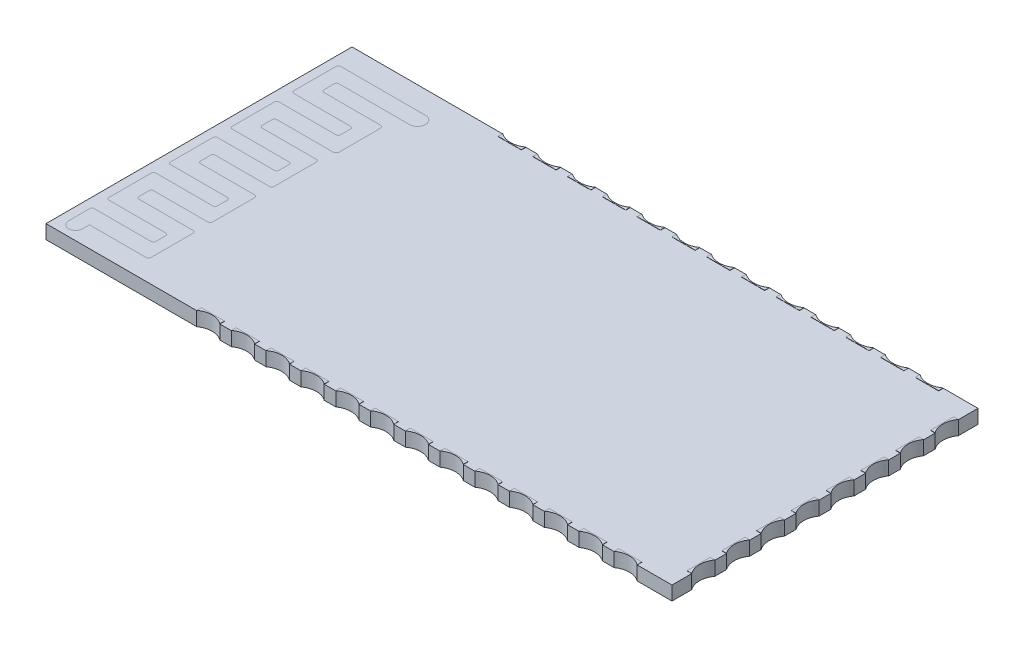
SolidWorks part; units mm, degrees
ref_plane "Front Plane" through (0, 0, 0) normal (0, 0, 1) x (1, 0, 0)
ref_plane "Top Plane" through (0, 0, 0) normal (0, 1, 0) x (1, 0, 0)
ref_plane "Right Plane" through (0, 0, 0) normal (1, 0, 0) x (0, 0, -1)
sketch "Sketch1" plane through (0, 0, 0) normal (0, 1, 0) x (1, 0, 0)
  line L1 (-13.5, -6.6) -> (13.5, -6.6)
  line L2 (-13.5, -6.6) -> (-13.5, 6.6)
  line L3 (-13.5, 6.6) -> (13.5, 6.6)
  line L4 (13.5, -6.6) -> (13.5, 6.6)
  line L5 (-13.5, -6.6) -> (13.5, 6.6) construction
  line L6 (-13.5, 6.6) -> (13.5, -6.6) construction
  point P0 (0, 0)
  dimension "D1" = 13.2
  dimension "D2" = 27
extrude "Boss-Extrude1" add sketch "Sketch1" along normal blind 0.6
sketch "Sketch2" plane through (0, 0.6, 0) normal (0, 1, 0) x (1, 0, 0)
  line L0 (-13.1181, -6.0063) -> (-13.1181, -5.0988)
  line L1 (-13.0181, -4.9988) -> (-10.5664, -4.9988)
  line L2 (-10.4664, -4.8988) -> (-10.4664, -4.4665)
  line L3 (-12.5181, -6.0063) -> (-12.5181, -5.7063)
  line L4 (-12.5181, -5.7063) -> (-10.0692, -5.7063)
  line L5 (-9.9692, -5.6063) -> (-9.9692, -3.7819)
  line L6 (-10.5664, -4.3665) -> (-13.0181, -4.3665)
  line L7 (-13.1181, -4.2665) -> (-13.1181, -2.4422)
  line L8 (-10.0692, -3.6819) -> (-12.4068, -3.6819)
  line L9 (-12.5068, -3.5819) -> (-12.5068, -3.1496)
  line L10 (-12.4068, -3.0496) -> (-10.0692, -3.0496)
  line L11 (-9.9692, -2.9496) -> (-9.9692, -1.1253)
  line L12 (-13.0181, -2.3422) -> (-10.5664, -2.3422)
  line L13 (-10.4664, -2.2422) -> (-10.4664, -1.8099)
  line L14 (-10.0692, -1.0253) -> (-12.4068, -1.0253)
  line L15 (-10.5664, -1.7099) -> (-13.0181, -1.7099)
  line L16 (-12.5068, -0.9253) -> (-12.5068, -0.493)
  line L17 (-13.1181, -1.6099) -> (-13.1181, 0.2145)
  line L18 (-13.0181, 0.3145) -> (-10.5664, 0.3145)
  line L19 (-12.4068, -0.393) -> (-10.0692, -0.393)
  line L20 (-9.9692, -0.293) -> (-9.9692, 1.5314)
  line L21 (-10.4664, 0.4145) -> (-10.4664, 0.8468)
  line L22 (-10.0692, 1.6314) -> (-12.4068, 1.6314)
  line L23 (-10.5664, 0.9468) -> (-13.0181, 0.9468)
  line L24 (-12.5068, 1.7314) -> (-12.5068, 2.1637)
  line L25 (-13.1181, 1.0468) -> (-13.1181, 2.8711)
  line L26 (-13.0181, 2.9711) -> (-10.5664, 2.9711)
  line L27 (-12.4068, 2.2637) -> (-9.9956, 2.2637)
  line L28 (-9.8488, 2.3826) -> (-9.8488, 4.2077)
  line L29 (-10.4664, 3.0711) -> (-10.4664, 3.5035)
  line L30 (-9.9832, 4.2909) -> (-12.4068, 4.2909)
  line L31 (-10.5664, 3.6035) -> (-13.0181, 3.6035)
  line L32 (-12.5068, 4.3909) -> (-12.5068, 4.8232)
  line L33 (-13.1181, 3.7035) -> (-13.1181, 5.5278)
  line L34 (-13.0181, 5.6278) -> (-9.358, 5.6278)
  line L35 (-12.4084, 4.9408) -> (-9.358, 4.9408)
  arc A0 (-13.1181, -6.0063) -> (-12.5181, -6.0063) centre (-12.8181, -6.0063) ccw
  arc A1 (-10.0692, -5.7063) -> (-9.9692, -5.6063) centre (-10.0692, -5.6063) ccw
  arc A2 (-13.1181, -5.0988) -> (-13.0181, -4.9988) centre (-13.0181, -5.0988) cw
  arc A3 (-10.5664, -4.9988) -> (-10.4664, -4.8988) centre (-10.5664, -4.8988) ccw
  arc A4 (-10.4664, -4.4665) -> (-10.5664, -4.3665) centre (-10.5664, -4.4665) ccw
  arc A5 (-9.9692, -3.7819) -> (-10.0692, -3.6819) centre (-10.0692, -3.7819) ccw
  arc A6 (-13.0181, -4.3665) -> (-13.1181, -4.2665) centre (-13.0181, -4.2665) cw
  arc A7 (-10.5664, -2.3422) -> (-10.4664, -2.2422) centre (-10.5664, -2.2422) ccw
  arc A8 (-10.0692, -3.0496) -> (-9.9692, -2.9496) centre (-10.0692, -2.9496) ccw
  arc A9 (-12.4068, -3.6819) -> (-12.5068, -3.5819) centre (-12.4068, -3.5819) cw
  arc A10 (-12.5068, -3.1496) -> (-12.4068, -3.0496) centre (-12.4068, -3.1496) cw
  arc A11 (-13.1181, -2.4422) -> (-13.0181, -2.3422) centre (-13.0181, -2.4422) cw
  arc A12 (-10.4664, -1.8099) -> (-10.5664, -1.7099) centre (-10.5664, -1.8099) ccw
  arc A13 (-9.9692, -1.1253) -> (-10.0692, -1.0253) centre (-10.0692, -1.1253) ccw
  arc A14 (-12.4068, -1.0253) -> (-12.5068, -0.9253) centre (-12.4068, -0.9253) cw
  arc A15 (-13.0181, -1.7099) -> (-13.1181, -1.6099) centre (-13.0181, -1.6099) cw
  arc A16 (-13.1181, 0.2145) -> (-13.0181, 0.3145) centre (-13.0181, 0.2145) cw
  arc A17 (-12.5068, -0.493) -> (-12.4068, -0.393) centre (-12.4068, -0.493) cw
  arc A18 (-10.0692, -0.393) -> (-9.9692, -0.293) centre (-10.0692, -0.293) ccw
  arc A19 (-10.5664, 0.3145) -> (-10.4664, 0.4145) centre (-10.5664, 0.4145) ccw
  arc A20 (-10.4664, 0.8468) -> (-10.5664, 0.9468) centre (-10.5664, 0.8468) ccw
  arc A21 (-9.9692, 1.5314) -> (-10.0692, 1.6314) centre (-10.0692, 1.5314) ccw
  arc A22 (-12.4068, 1.6314) -> (-12.5068, 1.7314) centre (-12.4068, 1.7314) cw
  arc A23 (-13.0181, 0.9468) -> (-13.1181, 1.0468) centre (-13.0181, 1.0468) cw
  arc A24 (-13.1181, 2.8711) -> (-13.0181, 2.9711) centre (-13.0181, 2.8711) cw
  arc A25 (-12.5068, 2.1637) -> (-12.4068, 2.2637) centre (-12.4068, 2.1637) cw
  arc A26 (-9.9956, 2.2637) -> (-9.8488, 2.3826) centre (-9.9956, 2.4138) ccw
  arc A27 (-10.5664, 2.9711) -> (-10.4664, 3.0711) centre (-10.5664, 3.0711) ccw
  arc A28 (-10.4664, 3.5035) -> (-10.5664, 3.6035) centre (-10.5664, 3.5035) ccw
  arc A29 (-9.8488, 4.2077) -> (-9.9832, 4.2909) centre (-9.9832, 4.1408) ccw
  arc A30 (-12.4068, 4.2909) -> (-12.5068, 4.3909) centre (-12.4068, 4.3909) cw
  arc A31 (-13.0181, 3.6035) -> (-13.1181, 3.7035) centre (-13.0181, 3.7035) cw
  arc A32 (-13.1181, 5.5278) -> (-13.0181, 5.6278) centre (-13.0181, 5.5278) cw
  arc A33 (-12.5068, 4.8232) -> (-12.4084, 4.9408) centre (-12.4084, 4.8408) cw
  arc A34 (-9.358, 4.9408) -> (-9.358, 5.6278) centre (-9.358, 5.2843) ccw
  dimension "D1" = 0.3
  dimension "D2" = 0.1
  dimension "D3" = 0.1
  dimension "D4" = 0.1
  dimension "D5" = 0.1
  dimension "D6" = 0.1
split line "Split Line1"
sketch "Sketch3" plane through (0, 0.6, 0) normal (0, 1, 0) x (1, 0, 0)
  line L0 (13.5, 6.6) -> (-13.5, 6.6) construction
  line L1 (-7, 6.6) -> (-6, 6.6)
  line L2 (-7, 6.6) -> (-7, 6.4)
  line L3 (-7, 6.4) -> (-6, 6.4)
  line L4 (-6, 6.6) -> (-6, 6.4)
  line L5 (-7, 6.6) -> (-6, 6.4) construction
  line L6 (-7, 6.4) -> (-6, 6.6) construction
  line L7 (-13.5, 6.6) -> (-13.5, -6.6) construction
  line L8 (-5.5, 6.6) -> (-5.5, 6.4)
  line L9 (-5.5, 6.6) -> (-4.5, 6.6)
  line L10 (-4.5, 6.6) -> (-4.5, 6.4)
  line L11 (-5.5, 6.4) -> (-4.5, 6.4)
  line L12 (-4, 6.6) -> (-4, 6.4)
  line L13 (-4, 6.6) -> (-3, 6.6)
  line L14 (-3, 6.6) -> (-3, 6.4)
  line L15 (-4, 6.4) -> (-3, 6.4)
  line L16 (-2.5, 6.6) -> (-2.5, 6.4)
  line L17 (-2.5, 6.6) -> (-1.5, 6.6)
  line L18 (-1.5, 6.6) -> (-1.5, 6.4)
  line L19 (-2.5, 6.4) -> (-1.5, 6.4)
  line L20 (-1, 6.6) -> (-1, 6.4)
  line L21 (-1, 6.6) -> (0, 6.6)
  line L22 (0, 6.6) -> (0, 6.4)
  line L23 (-1, 6.4) -> (0, 6.4)
  line L24 (0.5, 6.6) -> (0.5, 6.4)
  line L25 (0.5, 6.6) -> (1.5, 6.6)
  line L26 (1.5, 6.6) -> (1.5, 6.4)
  line L27 (0.5, 6.4) -> (1.5, 6.4)
  line L28 (2, 6.6) -> (2, 6.4)
  line L29 (2, 6.6) -> (3, 6.6)
  line L30 (3, 6.6) -> (3, 6.4)
  line L31 (2, 6.4) -> (3, 6.4)
  line L32 (3.5, 6.6) -> (3.5, 6.4)
  line L33 (3.5, 6.6) -> (4.5, 6.6)
  line L34 (4.5, 6.6) -> (4.5, 6.4)
  line L35 (3.5, 6.4) -> (4.5, 6.4)
  line L36 (5, 6.6) -> (5, 6.4)
  line L37 (5, 6.6) -> (6, 6.6)
  line L38 (6, 6.6) -> (6, 6.4)
  line L39 (5, 6.4) -> (6, 6.4)
  line L40 (6.5, 6.6) -> (6.5, 6.4)
  line L41 (6.5, 6.6) -> (7.5, 6.6)
  line L42 (7.5, 6.6) -> (7.5, 6.4)
  line L43 (6.5, 6.4) -> (7.5, 6.4)
  line L44 (8, 6.6) -> (8, 6.4)
  line L45 (8, 6.6) -> (9, 6.6)
  line L46 (9, 6.6) -> (9, 6.4)
  line L47 (8, 6.4) -> (9, 6.4)
  line L48 (9.5, 6.6) -> (9.5, 6.4)
  line L49 (9.5, 6.6) -> (10.5, 6.6)
  line L50 (10.5, 6.6) -> (10.5, 6.4)
  line L51 (9.5, 6.4) -> (10.5, 6.4)
  line L52 (11, 6.6) -> (11, 6.4)
  line L53 (11, 6.6) -> (12, 6.6)
  line L54 (12, 6.6) -> (12, 6.4)
  line L55 (11, 6.4) -> (12, 6.4)
  line L56 (13.5, -6.6) -> (13.5, 6.6) construction
  line L57 (13.5, 5.75) -> (13.3, 5.75)
  line L58 (13.5, 5.75) -> (13.5, 4.75)
  line L59 (13.5, 4.75) -> (13.3, 4.75)
  line L60 (13.3, 5.75) -> (13.3, 4.75)
  line L61 (13.5, 5.75) -> (13.3, 4.75) construction
  line L62 (13.5, 4.75) -> (13.3, 5.75) construction
  line L63 (13.5, 4.25) -> (13.5, 3.25)
  line L64 (13.5, 4.25) -> (13.3, 4.25)
  line L65 (13.3, 4.25) -> (13.3, 3.25)
  line L66 (13.5, 3.25) -> (13.3, 3.25)
  line L67 (13.5, 2.75) -> (13.5, 1.75)
  line L68 (13.5, 2.75) -> (13.3, 2.75)
  line L69 (13.3, 2.75) -> (13.3, 1.75)
  line L70 (13.5, 1.75) -> (13.3, 1.75)
  line L71 (13.5, 1.25) -> (13.5, 0.25)
  line L72 (13.5, 1.25) -> (13.3, 1.25)
  line L73 (13.3, 1.25) -> (13.3, 0.25)
  line L74 (13.5, 0.25) -> (13.3, 0.25)
  line L75 (13.5, -0.25) -> (13.5, -1.25)
  line L76 (13.5, -0.25) -> (13.3, -0.25)
  line L77 (13.3, -0.25) -> (13.3, -1.25)
  line L78 (13.5, -1.25) -> (13.3, -1.25)
  line L79 (13.5, -1.75) -> (13.5, -2.75)
  line L80 (13.5, -1.75) -> (13.3, -1.75)
  line L81 (13.3, -1.75) -> (13.3, -2.75)
  line L82 (13.5, -2.75) -> (13.3, -2.75)
  line L83 (13.5, -3.25) -> (13.5, -4.25)
  line L84 (13.5, -3.25) -> (13.3, -3.25)
  line L85 (13.3, -3.25) -> (13.3, -4.25)
  line L86 (13.5, -4.25) -> (13.3, -4.25)
  line L87 (13.5, -4.75) -> (13.5, -5.75)
  line L88 (13.5, -4.75) -> (13.3, -4.75)
  line L89 (13.3, -4.75) -> (13.3, -5.75)
  line L90 (13.5, -5.75) -> (13.3, -5.75)
  line L91 (0, 0) -> (-8.012, 0) construction
  line L92 (-7, -6.4) -> (-6, -6.6) construction
  line L93 (-7, -6.6) -> (-6, -6.4) construction
  line L94 (11, -6.4) -> (12, -6.4)
  line L95 (12, -6.6) -> (12, -6.4)
  line L96 (11, -6.6) -> (12, -6.6)
  line L97 (11, -6.6) -> (11, -6.4)
  line L98 (9.5, -6.4) -> (10.5, -6.4)
  line L99 (10.5, -6.6) -> (10.5, -6.4)
  line L100 (9.5, -6.6) -> (10.5, -6.6)
  line L101 (9.5, -6.6) -> (9.5, -6.4)
  line L102 (8, -6.4) -> (9, -6.4)
  line L103 (9, -6.6) -> (9, -6.4)
  line L104 (8, -6.6) -> (9, -6.6)
  line L105 (8, -6.6) -> (8, -6.4)
  line L106 (6.5, -6.4) -> (7.5, -6.4)
  line L107 (7.5, -6.6) -> (7.5, -6.4)
  line L108 (6.5, -6.6) -> (7.5, -6.6)
  line L109 (6.5, -6.6) -> (6.5, -6.4)
  line L110 (5, -6.4) -> (6, -6.4)
  line L111 (6, -6.6) -> (6, -6.4)
  line L112 (5, -6.6) -> (6, -6.6)
  line L113 (5, -6.6) -> (5, -6.4)
  line L114 (3.5, -6.4) -> (4.5, -6.4)
  line L115 (4.5, -6.6) -> (4.5, -6.4)
  line L116 (3.5, -6.6) -> (4.5, -6.6)
  line L117 (3.5, -6.6) -> (3.5, -6.4)
  line L118 (2, -6.4) -> (3, -6.4)
  line L119 (3, -6.6) -> (3, -6.4)
  line L120 (2, -6.6) -> (3, -6.6)
  line L121 (2, -6.6) -> (2, -6.4)
  line L122 (0.5, -6.4) -> (1.5, -6.4)
  line L123 (1.5, -6.6) -> (1.5, -6.4)
  line L124 (0.5, -6.6) -> (1.5, -6.6)
  line L125 (0.5, -6.6) -> (0.5, -6.4)
  line L126 (-1, -6.4) -> (0, -6.4)
  line L127 (0, -6.6) -> (0, -6.4)
  line L128 (-1, -6.6) -> (0, -6.6)
  line L129 (-1, -6.6) -> (-1, -6.4)
  line L130 (-2.5, -6.4) -> (-1.5, -6.4)
  line L131 (-1.5, -6.6) -> (-1.5, -6.4)
  line L132 (-2.5, -6.6) -> (-1.5, -6.6)
  line L133 (-2.5, -6.6) -> (-2.5, -6.4)
  line L134 (-4, -6.4) -> (-3, -6.4)
  line L135 (-3, -6.6) -> (-3, -6.4)
  line L136 (-4, -6.6) -> (-3, -6.6)
  line L137 (-4, -6.6) -> (-4, -6.4)
  line L138 (-5.5, -6.4) -> (-4.5, -6.4)
  line L139 (-4.5, -6.6) -> (-4.5, -6.4)
  line L140 (-5.5, -6.6) -> (-4.5, -6.6)
  line L141 (-5.5, -6.6) -> (-5.5, -6.4)
  line L142 (-6, -6.6) -> (-6, -6.4)
  line L143 (-7, -6.4) -> (-6, -6.4)
  line L144 (-7, -6.6) -> (-7, -6.4)
  line L145 (-7, -6.6) -> (-6, -6.6)
  point P4 (-6.5, 6.5)
  point P61 (13.4, 5.25)
  point P64 (13.4, 5.75)
  point P148 (-6.5, -6.5)
  dimension "D1" = 6.5
  dimension "D2" = 1
  dimension "D3" = 0.2
  dimension "D5" = 0.85
  dimension "D4" = 13
  dimension "D6" = 8
extrude "Boss-Extrude2" add sketch "Sketch3" along normal blind 0.01
sketch "Sketch4" plane through (0, 0.61, 0) normal (0, 1, 0) x (1, 0, 0)
  line L0 (-7, 6.6) -> (-6, 6.6)
  line L1 (-5.5, 6.6) -> (-4.5, 6.6)
  line L2 (-4, 6.6) -> (-3, 6.6)
  line L3 (-2.5, 6.6) -> (-1.5, 6.6)
  line L4 (-1, 6.6) -> (0, 6.6)
  line L5 (0.5, 6.6) -> (1.5, 6.6)
  line L6 (2, 6.6) -> (3, 6.6)
  line L7 (3.5, 6.6) -> (4.5, 6.6)
  line L8 (5, 6.6) -> (6, 6.6)
  line L9 (6.5, 6.6) -> (7.5, 6.6)
  line L10 (8, 6.6) -> (9, 6.6)
  line L11 (9.5, 6.6) -> (10.5, 6.6)
  line L12 (11, 6.6) -> (12, 6.6)
  line L13 (13.5, 5.75) -> (13.5, 4.75)
  line L14 (13.5, 4.25) -> (13.5, 3.25)
  line L15 (13.5, 2.75) -> (13.5, 1.75)
  line L16 (13.5, 1.25) -> (13.5, 0.25)
  line L17 (13.5, -0.25) -> (13.5, -1.25)
  line L18 (13.5, -1.75) -> (13.5, -2.75)
  line L19 (13.5, -3.25) -> (13.5, -4.25)
  line L20 (13.5, -4.75) -> (13.5, -5.75)
  line L22 (0, 0) -> (-8.8067, 0) construction
  line L23 (11, -6.6) -> (12, -6.6)
  line L24 (9.5, -6.6) -> (10.5, -6.6)
  line L25 (8, -6.6) -> (9, -6.6)
  line L26 (6.5, -6.6) -> (7.5, -6.6)
  line L27 (5, -6.6) -> (6, -6.6)
  line L28 (3.5, -6.6) -> (4.5, -6.6)
  line L29 (2, -6.6) -> (3, -6.6)
  line L30 (0.5, -6.6) -> (1.5, -6.6)
  line L31 (-1, -6.6) -> (0, -6.6)
  line L32 (-2.5, -6.6) -> (-1.5, -6.6)
  line L33 (-4, -6.6) -> (-3, -6.6)
  line L34 (-5.5, -6.6) -> (-4.5, -6.6)
  line L35 (-7, -6.6) -> (-6, -6.6)
  arc A0 (-7, 6.6) -> (-6, 6.6) centre (-6.5, 7.2874) ccw
  arc A1 (-5.5, 6.6) -> (-4.5, 6.6) centre (-5, 7.2874) ccw
  arc A2 (-4, 6.6) -> (-3, 6.6) centre (-3.5, 7.2874) ccw
  arc A3 (-2.5, 6.6) -> (-1.5, 6.6) centre (-2, 7.2874) ccw
  arc A4 (-1, 6.6) -> (0, 6.6) centre (-0.5, 7.2874) ccw
  arc A5 (0.5, 6.6) -> (1.5, 6.6) centre (1, 7.2874) ccw
  arc A6 (2, 6.6) -> (3, 6.6) centre (2.5, 7.2874) ccw
  arc A7 (3.5, 6.6) -> (4.5, 6.6) centre (4, 7.2874) ccw
  arc A8 (5, 6.6) -> (6, 6.6) centre (5.5, 7.2874) ccw
  arc A9 (6.5, 6.6) -> (7.5, 6.6) centre (7, 7.2874) ccw
  arc A10 (8, 6.6) -> (9, 6.6) centre (8.5, 7.2874) ccw
  arc A11 (9.5, 6.6) -> (10.5, 6.6) centre (10, 7.2874) ccw
  arc A12 (11, 6.6) -> (12, 6.6) centre (11.5, 7.2874) ccw
  arc A13 (13.5, 5.75) -> (13.5, 4.75) centre (14.1874, 5.25) ccw
  arc A14 (13.5, 4.25) -> (13.5, 3.25) centre (14.1874, 3.75) ccw
  arc A15 (13.5, 2.75) -> (13.5, 1.75) centre (14.1874, 2.25) ccw
  arc A16 (13.5, 1.25) -> (13.5, 0.25) centre (14.1874, 0.75) ccw
  arc A17 (13.5, -0.25) -> (13.5, -1.25) centre (14.1874, -0.75) ccw
  arc A18 (13.5, -1.75) -> (13.5, -2.75) centre (14.1874, -2.25) ccw
  arc A19 (13.5, -3.25) -> (13.5, -4.25) centre (14.1874, -3.75) ccw
  arc A20 (13.5, -4.75) -> (13.5, -5.75) centre (14.1874, -5.25) ccw
  arc A21 (11, -6.6) -> (12, -6.6) centre (11.5, -7.2874) cw
  arc A22 (9.5, -6.6) -> (10.5, -6.6) centre (10, -7.2874) cw
  arc A23 (8, -6.6) -> (9, -6.6) centre (8.5, -7.2874) cw
  arc A24 (6.5, -6.6) -> (7.5, -6.6) centre (7, -7.2874) cw
  arc A25 (5, -6.6) -> (6, -6.6) centre (5.5, -7.2874) cw
  arc A26 (3.5, -6.6) -> (4.5, -6.6) centre (4, -7.2874) cw
  arc A27 (2, -6.6) -> (3, -6.6) centre (2.5, -7.2874) cw
  arc A28 (0.5, -6.6) -> (1.5, -6.6) centre (1, -7.2874) cw
  arc A29 (-1, -6.6) -> (0, -6.6) centre (-0.5, -7.2874) cw
  arc A30 (-2.5, -6.6) -> (-1.5, -6.6) centre (-2, -7.2874) cw
  arc A31 (-4, -6.6) -> (-3, -6.6) centre (-3.5, -7.2874) cw
  arc A32 (-5.5, -6.6) -> (-4.5, -6.6) centre (-5, -7.2874) cw
  arc A33 (-7, -6.6) -> (-6, -6.6) centre (-6.5, -7.2874) cw
  dimension "D1" = 0.85
  dimension "D3" = 0.85
  dimension "D2" = 13
  dimension "D4" = 8
extrude "Cut-Extrude1" cut sketch "Sketch4" against normal through all
